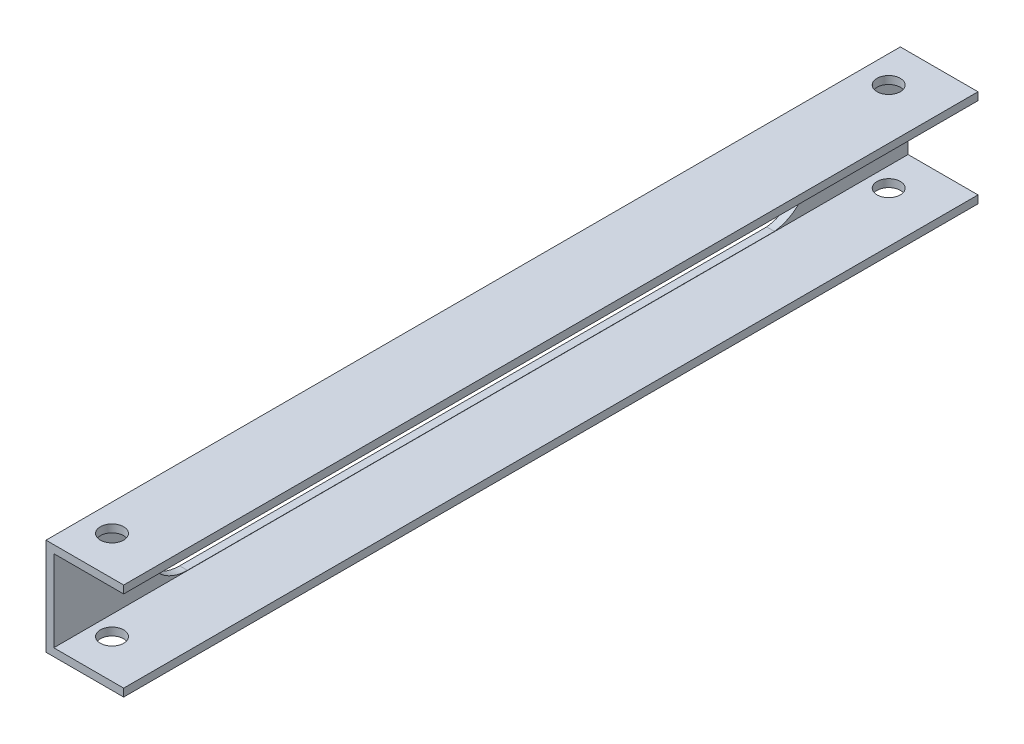
SolidWorks part; units mm, degrees
ref_plane "Front Plane" through (0, 0, 0) normal (0, 0, 1) x (1, 0, 0)
ref_plane "Top Plane" through (0, 0, 0) normal (0, 1, 0) x (1, 0, 0)
ref_plane "Right Plane" through (0, 0, 0) normal (1, 0, 0) x (0, 0, -1)
sketch "Sketch1" plane through (0, 0, 0) normal (0, 0, 1) x (1, 0, 0)
  line L0 (-157.7034, 227.1369) -> (-157.7034, 225.1369)
  line L1 (-177.7034, 250.1369) -> (-157.7034, 250.1369)
  line L2 (-177.7034, 250.1369) -> (-177.7034, 225.1369)
  line L3 (-177.7034, 225.1369) -> (-157.7034, 225.1369)
  line L4 (-157.7034, 250.1369) -> (-157.7034, 248.1369)
  line L9 (-157.7034, 248.1369) -> (-175.7034, 248.1369)
  line L11 (-157.7034, 227.1369) -> (-175.7034, 227.1369)
  line L12 (-175.7034, 248.1369) -> (-175.7034, 227.1369)
  dimension "D1" = 20
  dimension "D2" = 25
  dimension "D3" = 2
  dimension "D4" = 2
extrude "Boss-Extrude1" add sketch "Sketch1" along normal blind 220
sketch "Sketch2" plane through (-177.7034, 0, 0) normal (-1, 0, 0) x (0, 0, 1)
  line L1 (34.4067, 248.0696) -> (185.5933, 248.0696)
  line L3 (34.4067, 227.2041) -> (185.5933, 227.2041)
  line L6 (185.5933, 237.6369) -> (35.5933, 237.6369) construction
  line L8 (220, 250.1369) -> (0, 250.1369) construction
  line L9 (220, 225.1369) -> (0, 225.1369) construction
  line L10 (110, 248.0696) -> (110, 227.2041) construction
  line L11 (0, 250.1369) -> (0, 225.1369) construction
  line L12 (220, 250.1369) -> (220, 225.1369) construction
  arc A0 (34.4067, 248.0696) -> (34.4067, 227.2041) centre (35.5933, 237.6369) ccw
  arc A1 (185.5933, 227.2041) -> (185.5933, 248.0696) centre (185.5933, 237.6369) ccw
  dimension "D1" = 10.5
  dimension "D2" = 150
extrude "Cut-Extrude1" cut sketch "Sketch2" against normal up to next
sketch "Sketch3" plane through (0, 250.1369, 0) normal (0, 1, 0) x (1, 0, 0)
  line L0 (-177.7034, -220) -> (-177.7034, 0) construction
  line L1 (-170.7034, -210) -> (-170.7034, -10) construction
  line L2 (-170.7034, -110) -> (-177.7034, -110) construction
  line L3 (-157.7034, -220) -> (-177.7034, -220) construction
  line L4 (-157.7034, 0) -> (-177.7034, 0) construction
  circle A0 centre (-170.7034, -210) radius 3
  circle A2 centre (-170.7034, -10) radius 3
  dimension "D3" = 6
  dimension "D1" = 200
  dimension "D2" = 7
extrude "Cut-Extrude2" cut sketch "Sketch3" against normal blind 220
equation "\"D4@Sketch1\"=\"D3@Sketch1\""
